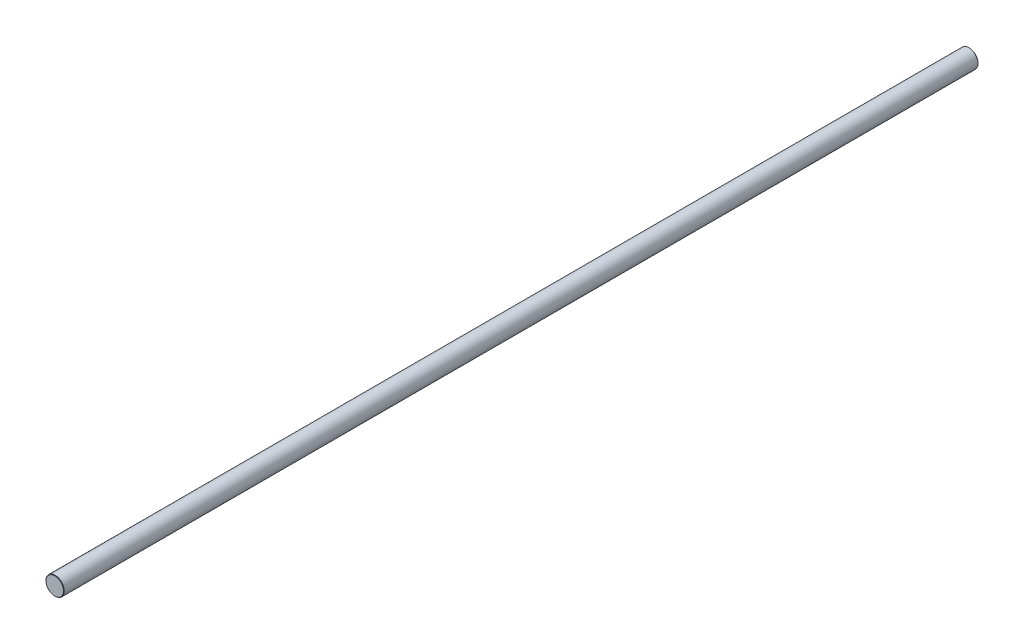
SolidWorks part; units mm, degrees
ref_plane "Front Plane" through (0, 0, 0) normal (0, 0, 1) x (1, 0, 0)
ref_plane "Top Plane" through (0, 0, 0) normal (0, 1, 0) x (1, 0, 0)
ref_plane "Right Plane" through (0, 0, 0) normal (1, 0, 0) x (0, 0, -1)
sketch "Sketch1" plane through (0, 0, 0) normal (0, 0, 1) x (1, 0, 0)
  circle A0 centre (0, 0) radius 10 construction
  dimension "Diameter" = 20
sketch "Sketch2" plane through (0, 0, 0) normal (1, 0, 0) x (0, 0, -1)
  line L0 (500, 0) -> (-500, 0) construction
  point P0 (-400, 0)
  point P3 (0, 0)
  point P4 (400, 0)
  point P6 (-350, 0)
  point P7 (350, 0)
  dimension "Length" = 1000
  dimension "D1" = 100
  dimension "D2" = 100
  dimension "D3" = 150
  dimension "D4" = 150
sketch "Sketch3" plane through (0, 0, 0) normal (0, 0, 1) x (1, 0, 0)
  circle A0 centre (0, 0) radius 10 construction
  circle A1 centre (0, 0) radius 10
extrude "Boss-Extrude1" add sketch "Sketch3" along normal up to vertex (500 mm away) and the other way up to vertex (500 mm away) up to point (0, 0, 500) other way up to point (0, 0, -500)
chamfer "Chamfer1" distance 0.4 angle 45 2 edges at (10, 0, 500) (10, 0, -500)
equation "\"D1@Chamfer1\"=\"Diameter@Sketch1\"*.02"
equation "\"D1@Sketch2\"=\"D2@Sketch2\""
equation "\"D2@Sketch2\"=\"Length@Sketch2\"*.1"
equation "\"D3@Sketch2\"=\"Length@Sketch2\"*.15"
equation "\"D4@Sketch2\"=\"D3@Sketch2\""
